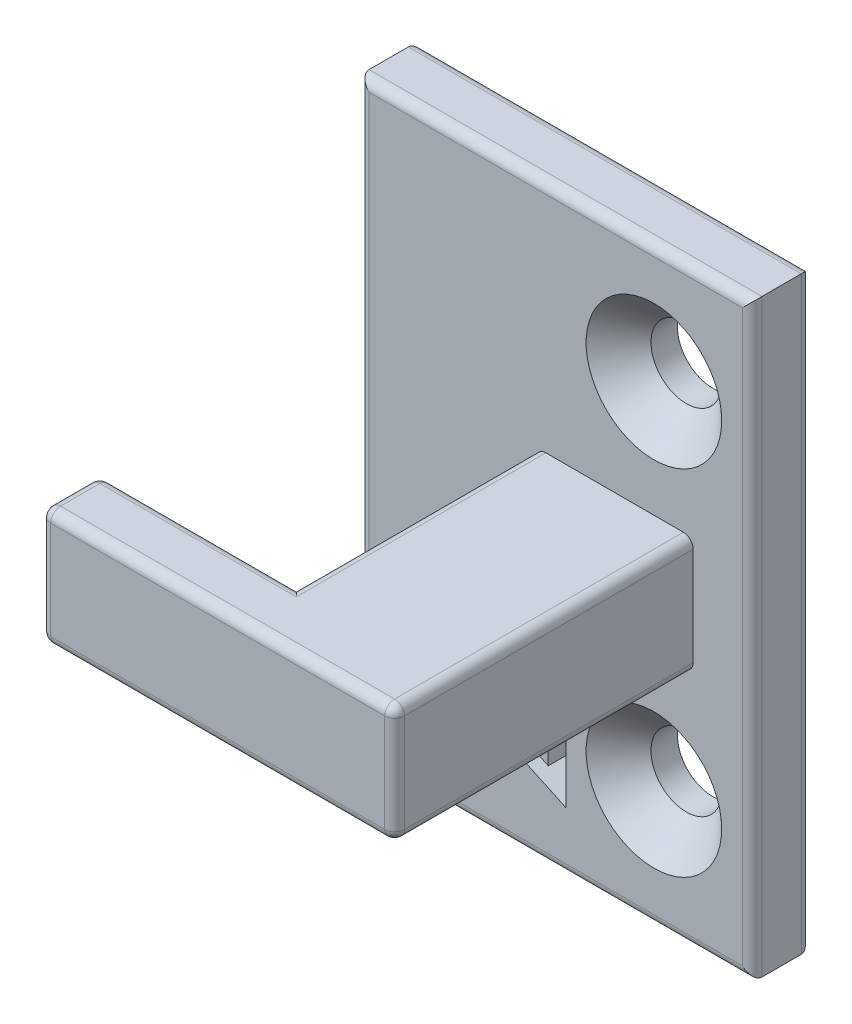
SolidWorks part; units mm, degrees
ref_plane "Front Plane" through (0, 0, 0) normal (0, 0, 1) x (1, 0, 0)
ref_plane "Top Plane" through (0, 0, 0) normal (0, 1, 0) x (1, 0, 0)
ref_plane "Right Plane" through (0, 0, 0) normal (1, 0, 0) x (0, 0, -1)
sketch "Sketch1" plane through (0, 0, 0) normal (0, 0, 1) x (1, 0, 0)
  line L1 (10, -15) -> (-10, -15)
  line L2 (10, -15) -> (10, 15)
  line L3 (10, 15) -> (-10, 15)
  line L4 (-10, -15) -> (-10, 15)
  line L5 (10, -15) -> (-10, 15) construction
  line L6 (10, 15) -> (-10, -15) construction
  point P0 (0, 0)
  dimension "D1" = 20
  dimension "D2" = 30
extrude "Boss-Extrude1" add sketch "Sketch1" along normal blind 3
sketch "Sketch2" plane through (0, 0, 3) normal (0, 0, 1) x (1, 0, 0)
  line L0 (5, 9) -> (5, -9) construction
  line L1 (-10, 15) -> (-10, -15) construction
  point P0 (5, 9)
  point P1 (5, -9)
  point P4 (5, 0)
  point P7 (-10, 0)
  dimension "D1" = 18
  dimension "D2" = 15
hole_wizard "CSK for M3 Countersunk Flat Head Screw1" positions "3DSketch1" profile "Sketch3" countersink size "M3" standard "DIN"
sketch3d "3DSketch1"
  point P0 (5, 9, 3)
  point P3 (5, -9, 3)
sketch "Sketch3" plane through (5, 9, 3) normal (1, 0, 0) x (0, -1, 0)
  line L0 (0, 0) -> (0, 21.0815)
  line L1 (0, 21.0815) -> (1.8, 20)
  line L2 (1.8, 20) -> (1.8, 1.65)
  line L3 (1.8, 1.65) -> (3.45, 0)
  line L5 (3.45, 0) -> (0, 0)
  line L6 (-1.8, 1.65) -> (-3.45, 0) construction
  line L10 (0, 21.0815) -> (-1.8, 20) construction
  line L11 (0, -6.35) -> (0, 107.95) construction
  dimension "Hole Dia." = 3.6
  dimension "Hole Depth" = 20
  dimension "Near C'Sink Dia." = 6.9
  dimension "Near C'Sink Angle" = 90
  dimension "Drill Angle" = 118
sketch "Sketch4" plane through (0, 0, 3) normal (0, 0, 1) x (1, 0, 0)
  line L0 (10, -15) -> (10, 15) construction
  line L1 (7, 3.1085) -> (-1, 3.1085)
  line L2 (7, 3.1085) -> (7, -2.8915)
  line L3 (7, -2.8915) -> (-1, -2.8915)
  line L4 (-1, 3.1085) -> (-1, -2.8915)
  line L5 (7, 3.1085) -> (-1, -2.8915) construction
  line L6 (7, -2.8915) -> (-1, 3.1085) construction
  point P0 (3, 0.1085)
  dimension "D1" = 6
  dimension "D2" = 8
  dimension "D3" = 3
extrude "Boss-Extrude2" add sketch "Sketch4" along normal blind 15.2
sketch "Sketch5" plane through (-1, 0, 0) normal (-1, 0, 0) x (0, 0, 1)
  line L0 (18.2, -2.8915) -> (3, -2.8915) construction
  line L1 (18.2, 3.1085) -> (15.2, 3.1085)
  line L2 (18.2, 3.1085) -> (18.2, -2.8915)
  line L3 (18.2, -2.8915) -> (15.2, -2.8915)
  line L4 (15.2, 3.1085) -> (15.2, -2.8915)
  dimension "D1" = 3
extrude "Boss-Extrude3" add sketch "Sketch5" along normal blind 10
fillet "Fillet2" radius 0.5 17 edges at (10, 0, 0) (10, 0, 3) (0, -15, 3) (0, -15, 0) (-10, 0, 0) (0, 15, 0) (0, 15, 3) (-10, 0, 3) (-1, -2.8915, 9.1) (-6, -2.8915, 15.2) (-2, -2.8915, 18.2) (-2, 3.1085, 18.2) (-6, 3.1085, 15.2) (7, -2.8915, 10.6) (7, 3.1085, 10.6) (-1, 3.1085, 9.1) (7, 0.1085, 18.2)
sketch "Sketch6" plane through (0, 0, 3) normal (0, 0, 1) x (1, 0, 0)
  line L0 (-7.399, 13.6207) -> (-7.399, -14.1695) construction
  text T0 "      Z" font "Century Gothic" height in points 30
  point P2 (-7.399, -14.1695)
extrude "Cut-Extrude1" cut sketch "Sketch6" against normal through all
fillet "Fillet3" radius 0.5 8 edges at (-11, -2.7451, 18.0536) (-11, -2.7451, 15.3464) (-11, 2.962, 15.3464) (-11, 2.962, 18.0536) (-11, -2.8915, 16.7) (-11, 0.1085, 15.2) (-11, 3.1085, 16.7) (-11, 0.1085, 18.2)
